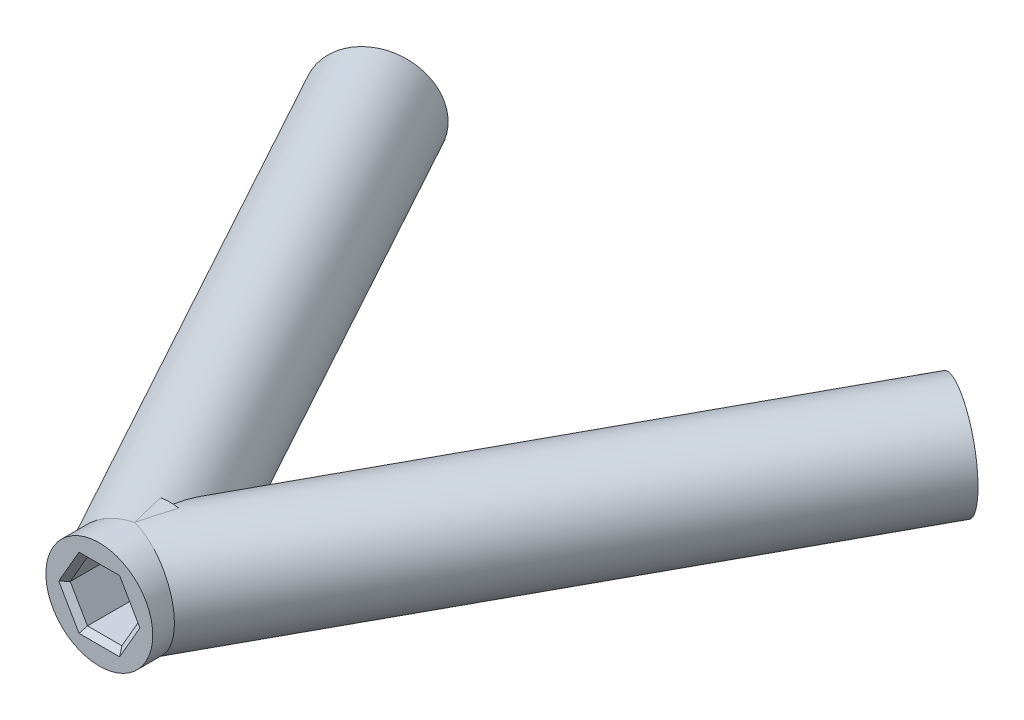
SolidWorks part; units mm, degrees
material "ABS"
ref_plane "Front Plane" through (0, 0, 0) normal (0, 0, 1) x (1, 0, 0)
ref_plane "Top Plane" through (0, 0, 0) normal (0, 1, 0) x (1, 0, 0)
ref_plane "Right Plane" through (0, 0, 0) normal (1, 0, 0) x (0, 0, -1)
sketch "Sketch1" plane through (0, 0, 0) normal (0, 1, 0) x (1, 0, 0)
  line L0 (0, 0) -> (-35.5851, 85.91) construction
  line L1 (0, 0) -> (35.5851, 85.91) construction
  line L2 (0, 0) -> (0, 85.91) construction
  line L3 (0, 17.5) -> (0, 24.1)
  line L4 (-35.5851, 85.91) -> (0, 20.8) construction
  line L5 (0, 20.8) -> (35.5851, 85.91) construction
  point P3 (0, 17.5)
  point P6 (-35.5851, 85.91)
  point P7 (35.5851, 85.91)
  point P10 (0, 20.8)
  point P13 (27.1924, 70.5538)
  point P15 (-27.1924, 70.5538)
  dimension "D1" = 45
  dimension "D2" = 85.91
  dimension "D3" = 17.5
  dimension "D4" = 17.5
  dimension "D5" = 17.5
  dimension "D6" = 6.6
  dimension "D7" = 57.317
  dimension "D8" = 74.1998
  dimension "D9" = 74.1998
revolve "Revolve-Thin1" add sketch "Sketch1" angle 360 about L2 wall 5
sketch "Sketch3" plane through (0, 0, 0) normal (0, 1, 0) x (1, 0, 0)
  line L1 (-27.1924, 70.5538) -> (0, 20.8)
  line L2 (0, 17.5) -> (0, 24.1) construction
revolve "Revolve-Thin4" add sketch "Sketch3" angle 360 about L1 wall 5
sketch "Sketch4" plane through (0, 0, 0) normal (0, 1, 0) x (1, 0, 0)
  line L0 (0, 20.8) -> (35.5851, 85.91) construction
  line L1 (0, 20.8) -> (27.1924, 70.5538)
  point P2 (27.1924, 70.5538)
revolve "Revolve-Thin3" add sketch "Sketch4" angle 360 about L1 wall 5
sketch "Sketch6" plane through (0, 0, -17.5) normal (0, 0, 1) x (1, 0, 0)
  line L1 (1.6108, 2.79) -> (-1.6108, 2.79)
  line L2 (-1.6108, 2.79) -> (-3.2216, 0)
  line L3 (-3.2216, 0) -> (-1.6108, -2.79)
  line L4 (-1.6108, -2.79) -> (1.6108, -2.79)
  line L5 (1.6108, -2.79) -> (3.2216, 0)
  line L6 (3.2216, 0) -> (1.6108, 2.79)
  circle A0 centre (0, 0) radius 2.79 construction
  dimension "D1" = 5.58
extrude "Cut-Extrude2" cut sketch "Sketch6" against normal blind 6.6
sketch "Sketch7" plane through (35.9457, 0, -65.7698) normal (0.4796, 0, -0.8775) x (-0.8775, 0, -0.4796)
  line L0 (9.9754, 5) -> (9.9754, -5) construction
  line L1 (7.0216, 1.2862) -> (7.3846, -1.9149)
  line L2 (7.3846, -1.9149) -> (10.3383, -3.2011)
  line L3 (10.3383, -3.2011) -> (12.9291, -1.2862)
  line L4 (12.9291, -1.2862) -> (12.5661, 1.9149)
  line L5 (12.5661, 1.9149) -> (9.6124, 3.2011)
  line L6 (9.6124, 3.2011) -> (7.0216, 1.2862)
  line L7 (4.9754, 0) -> (14.9754, 0) construction
  line L8 (9.6124, 3.2011) -> (10.3383, -3.2011) construction
  circle A0 centre (9.9754, 0) radius 2.79 construction
  circle A1 centre (9.9754, 0) radius 5 construction
  arc A2 (9.9754, 5) -> (9.9754, -5) centre (9.9754, 0) ccw construction
  dimension "D1" = 5.58
  dimension "D2" = 6.469
extrude "Cut-Extrude3" cut sketch "Sketch7" against normal blind 6.6
sketch "Sketch8" plane through (-35.9457, 0, -65.7698) normal (-0.4796, 0, -0.8775) x (-0.8775, 0, 0.4796)
  line L0 (-9.9754, 5) -> (-9.9754, -5) construction
  line L1 (-9.6124, 3.2011) -> (-12.5661, 1.9149)
  line L2 (-12.5661, 1.9149) -> (-12.9291, -1.2862)
  line L3 (-12.9291, -1.2862) -> (-10.3383, -3.2011)
  line L4 (-10.3383, -3.2011) -> (-7.3846, -1.9149)
  line L5 (-7.3846, -1.9149) -> (-7.0216, 1.2862)
  line L6 (-7.0216, 1.2862) -> (-9.6124, 3.2011)
  circle A0 centre (-9.9754, 0) radius 2.79 construction
  circle A1 centre (-9.9754, 0) radius 5 construction
  dimension "D1" = 5.58
  dimension "D2" = 6.469
extrude "Cut-Extrude4" cut sketch "Sketch8" against normal blind 6.6
chamfer "Chamfer1" distance 0.5 angle 45 18 edges at (-24.7597, 0.3143, -71.8833) (-25.7372, -2.2437, -71.3491) (-28.1698, -2.558, -70.0196) (-29.625, -0.3143, -69.2243) (-28.6476, 2.2437, -69.7585) (-26.2149, 2.558, -71.088) (-2.4162, 1.395, -17.5) (-2.4162, -1.395, -17.5) (0, -2.79, -17.5) (2.4162, -1.395, -17.5) (2.4162, 1.395, -17.5) (0, 2.79, -17.5) (24.7597, 0.3143, -71.8833) (26.2149, 2.558, -71.088) (28.6476, 2.2437, -69.7585) (29.625, -0.3143, -69.2243) (28.1698, -2.558, -70.0196) (25.7372, -2.2437, -71.3491)
